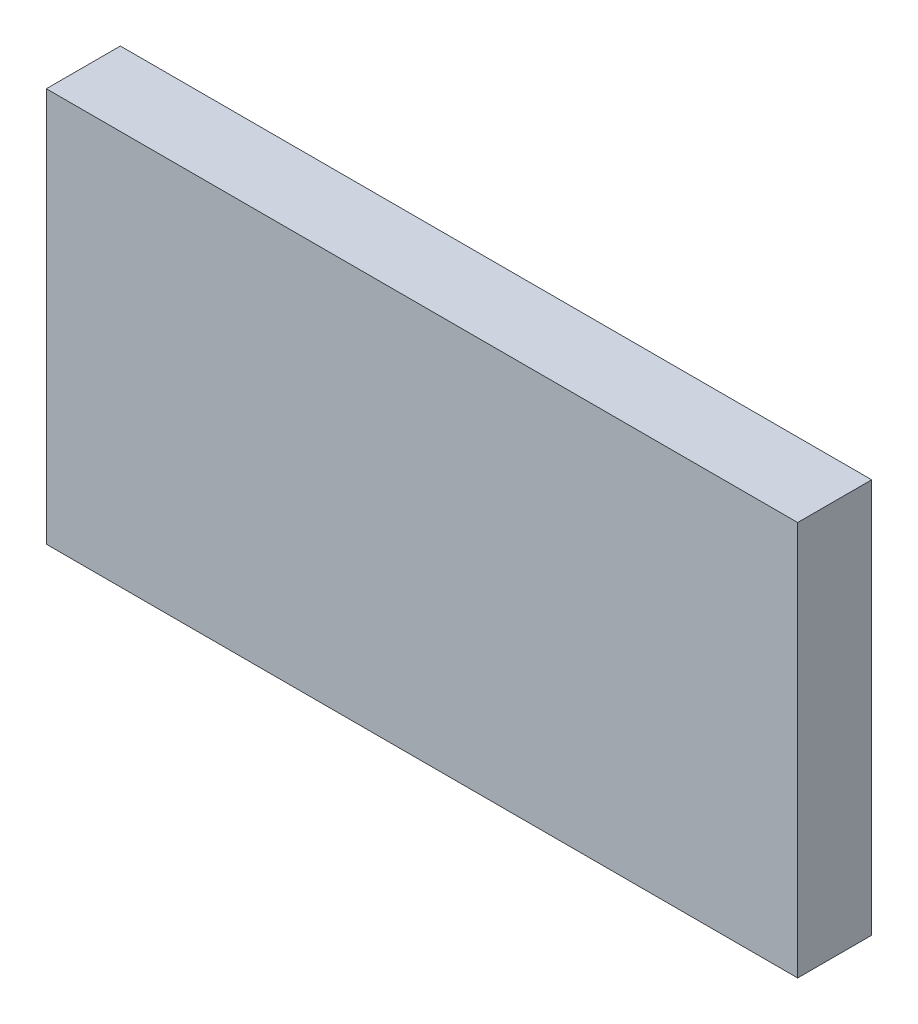
SolidWorks part; units mm, degrees
ref_plane "Front" through (0, 0, 0) normal (0, 0, 1) x (1, 0, 0)
ref_plane "Top" through (0, 0, 0) normal (0, 1, 0) x (1, 0, 0)
ref_plane "Right" through (0, 0, 0) normal (1, 0, 0) x (0, 0, -1)
sketch "Esquisse1" plane through (0, 0, 0) normal (0, 0, 1) x (1, 0, 0)
  line L1 (-50.76, 26.65) -> (50.76, 26.65)
  line L2 (-50.76, 26.65) -> (-50.76, -26.65)
  line L3 (-50.76, -26.65) -> (50.76, -26.65)
  line L4 (50.76, 26.65) -> (50.76, -26.65)
  point P4 (0, 26.65)
  point P6 (50.76, 0)
  dimension "D1" = 101.52
  dimension "D2" = 53.3
extrude "Boss.-Extru.1" add sketch "Esquisse1" along normal blind 10
